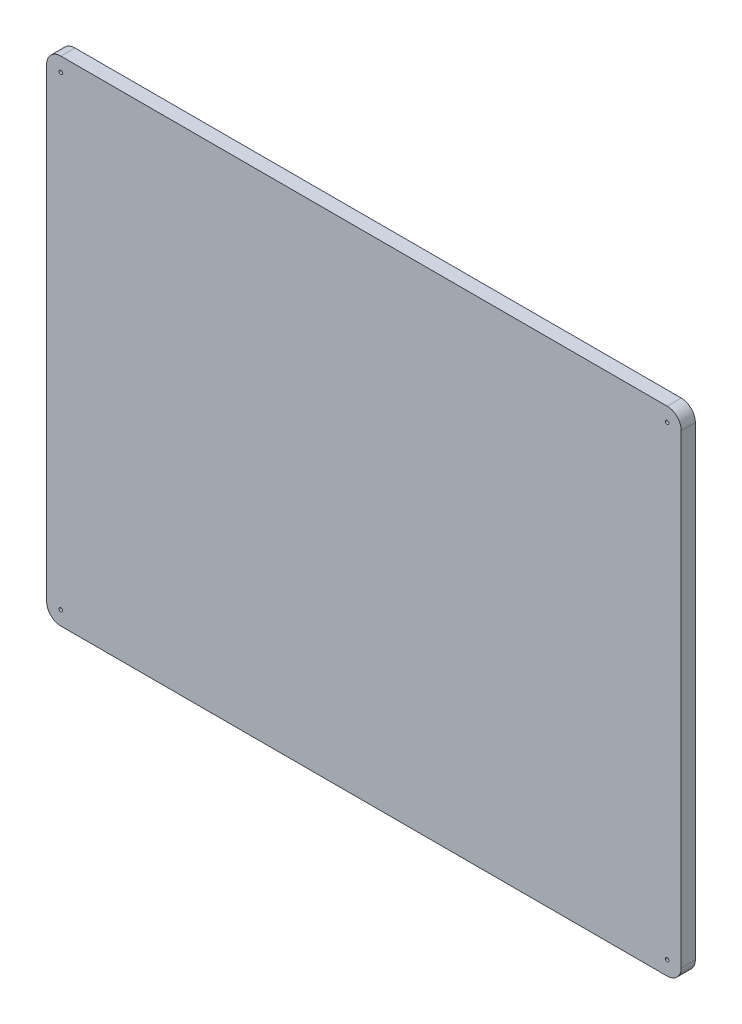
SolidWorks part; units mm, degrees
ref_plane "Front Plane" through (0, 0, 0) normal (0, 0, 1) x (1, 0, 0)
ref_plane "Top Plane" through (0, 0, 0) normal (0, 1, 0) x (1, 0, 0)
ref_plane "Right Plane" through (0, 0, 0) normal (1, 0, 0) x (0, 0, -1)
sketch "Sketch1" plane through (0, 0, 0) normal (0, 0, 1) x (1, 0, 0)
  line L0 (57.15, -41.91) -> (57.15, 41.91) construction
  line L1 (-57.15, -44.45) -> (57.15, -44.45)
  line L2 (-57.15, -44.45) -> (-57.15, 44.45)
  line L3 (-57.15, 44.45) -> (57.15, 44.45)
  line L4 (57.15, -44.45) -> (57.15, 44.45)
  line L5 (-57.15, -44.45) -> (57.15, 44.45) construction
  line L6 (-57.15, 44.45) -> (57.15, -44.45) construction
  line L7 (54.61, 44.45) -> (-54.61, 44.45) construction
  point P0 (0, 0)
extrude "Boss-Extrude1" add sketch "Sketch1" along normal blind 2.54
fillet "Fillet1" radius 2.54 4 edges at (-57.15, -44.45, 1.27) (-57.15, 44.45, 1.27) (57.15, 44.45, 1.27) (57.15, -44.45, 1.27)
sketch "Sketch2" plane through (0, 0, 2.54) normal (0, 0, 1) x (1, 0, 0)
  circle A0 centre (-54.61, 41.91) radius 0.3175
  circle A1 centre (54.61, 41.91) radius 0.3175
  circle A2 centre (54.61, -41.91) radius 0.3175
  circle A3 centre (-54.61, -41.91) radius 0.3175
  dimension "D1" = 0.635
extrude "Cut-Extrude1" cut sketch "Sketch2" against normal up to next
